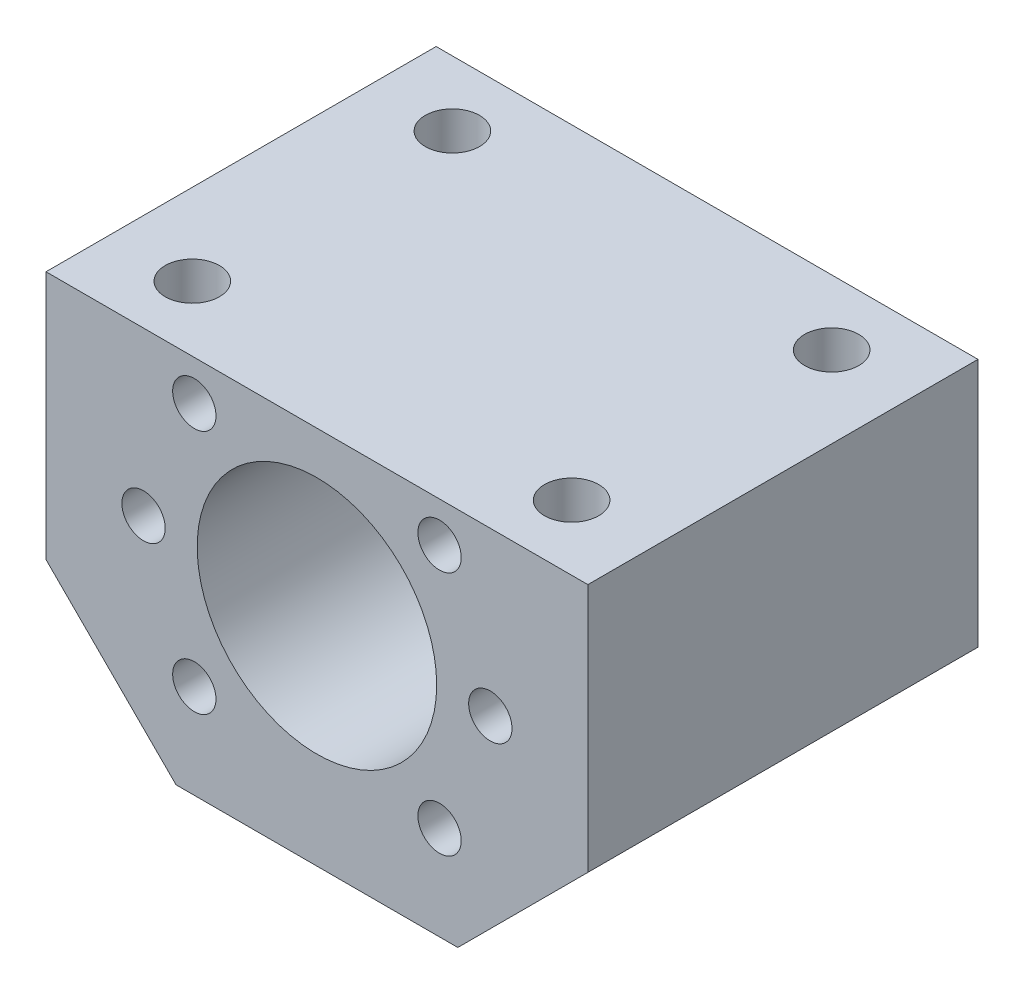
SolidWorks part; units mm, degrees
material "6061 合金"
ref_plane "前视基准面" through (0, 0, 0) normal (0, 0, 1) x (1, 0, 0)
ref_plane "上视基准面" through (0, 0, 0) normal (0, 1, 0) x (1, 0, 0)
ref_plane "右视基准面" through (0, 0, 0) normal (1, 0, 0) x (0, 0, -1)
sketch "草图1" plane through (0, 0, 0) normal (0, 0, 1) x (1, 0, 0)
  line L0 (0, 24.6031) -> (0, -23.325) construction
  line L1 (-29.6355, 0) -> (26.1208, 0) construction
  line L2 (25, 15) -> (-25, 15)
  line L3 (-25, 15) -> (-25, -8)
  line L4 (-25, -8) -> (-13, -20)
  line L5 (-13, -20) -> (13, -20)
  line L6 (25, -8) -> (13, -20)
  line L7 (25, 15) -> (25, -8)
  circle A0 centre (0, 0) radius 11.05
  circle A1 centre (0, 0) radius 16 construction
  circle A2 centre (-16, 0) radius 2
  circle A3 centre (-11.3137, 11.3137) radius 2
  circle A4 centre (-11.3137, -11.3137) radius 2
  circle A5 centre (11.3137, -11.3137) radius 2
  circle A6 centre (11.3137, 11.3137) radius 2
  circle A7 centre (16, 0) radius 2
  point P14 (0, -20)
  point P16 (0, 15)
  dimension "D1" = 22.1
  dimension "D7" = 32
  dimension "D8" = 4
  dimension "D2" = 35
  dimension "D3" = 15
  dimension "D4" = 50
  dimension "D5" = 12
  dimension "D6" = 12
  dimension "D9" = 90
extrude "凸台-拉伸1" add sketch "草图1" along normal blind 36
sketch "草图3" plane through (0, 15, 0) normal (0, 1, 0) x (1, 0, 0)
  line L0 (0, 0) -> (0, -36) construction
  line L1 (25, 0) -> (-25, 0) construction
  line L2 (25, -36) -> (-25, -36) construction
  circle A0 centre (-17.5, -6) radius 2.5
  circle A1 centre (-17.5, -30) radius 2.5
  circle A2 centre (17.5, -30) radius 2.5
  circle A3 centre (17.5, -6) radius 2.5
  dimension "D1" = 5
  dimension "D2" = 6
  dimension "D3" = 24
  dimension "D4" = 35
extrude "切除-拉伸1" cut sketch "草图3" against normal blind 10
